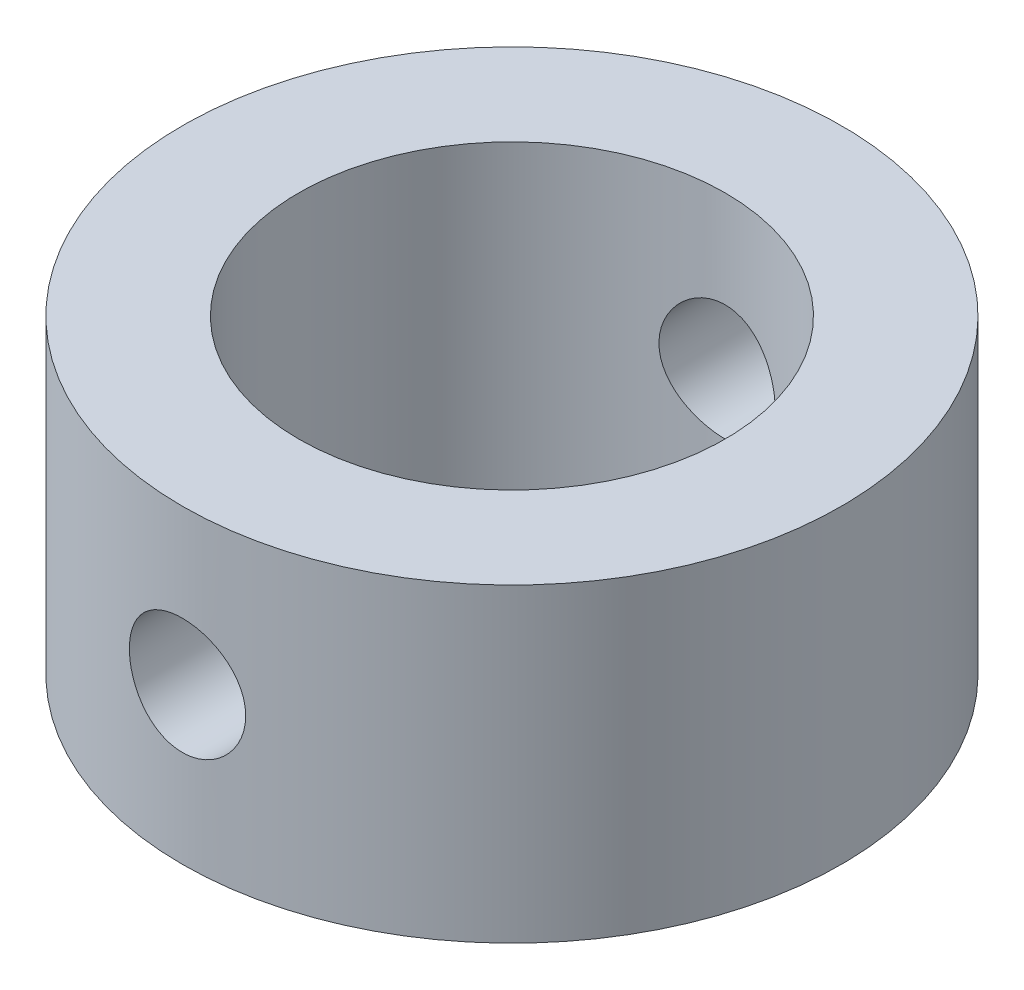
SolidWorks part; units mm, degrees
ref_plane "Front Plane" through (0, 0, 0) normal (0, 0, 1) x (1, 0, 0)
ref_plane "Top Plane" through (0, 0, 0) normal (0, 1, 0) x (1, 0, 0)
ref_plane "Right Plane" through (0, 0, 0) normal (1, 0, 0) x (0, 0, -1)
sketch "Sketch1" plane through (0, 0, 0) normal (0, 1, 0) x (1, 0, 0)
  circle A0 centre (0, 0) radius 53.975
extrude "Boss-Extrude1" add sketch "Sketch1" along normal blind 50.8
sketch "Sketch2" plane through (0, 50.8, 0) normal (0, 1, 0) x (1, 0, 0)
  circle A0 centre (0, 0) radius 34.925
extrude "Cut-Extrude1" cut sketch "Sketch2" against normal through all
sketch3d "3DSketch1" plane through (0, 0, 0) normal (0, 0, 1) x (1, 0, 0)
sketch3d "3DSketch2" plane through (0, 0, 0) normal (0, 0, 1) x (1, 0, 0)
sketch "Sketch4" plane through (0, 0, 0) normal (0, 0, 1) x (1, 0, 0)
  line L0 (-53.975, 0) -> (53.975, 0) construction
  circle A0 centre (0, 25.4) radius 9.525
  dimension "D1" = 25.4
extrude "Cut-Extrude3" cut sketch "Sketch4" against normal through all and the other way through all
